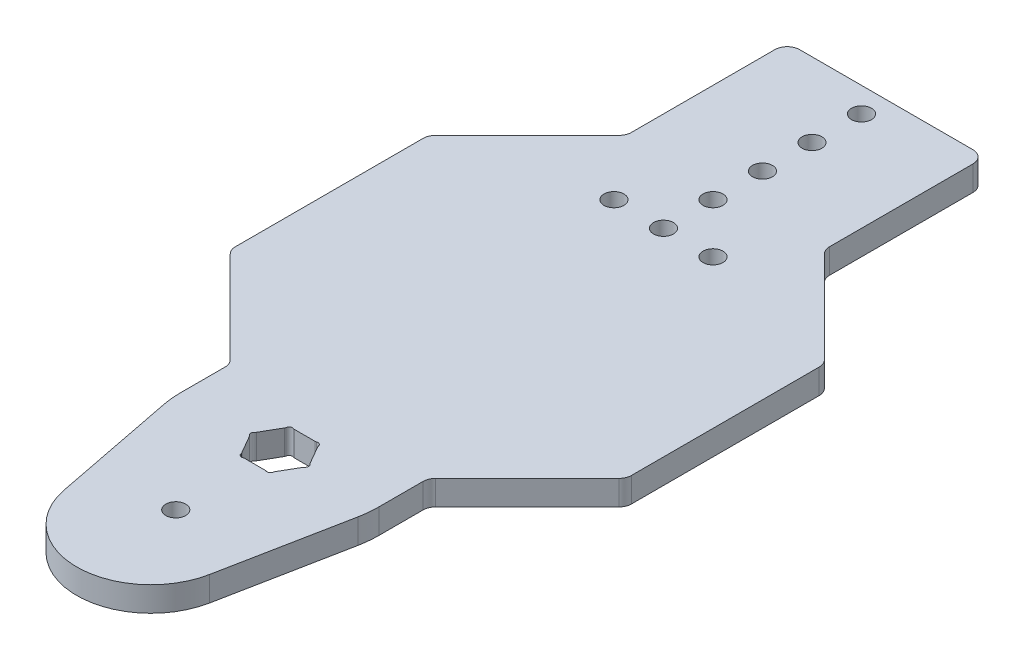
SolidWorks part; units mm, degrees
ref_plane "Front Plane" through (0, 0, 0) normal (0, 0, 1) x (1, 0, 0)
ref_plane "Top Plane" through (0, 0, 0) normal (0, 1, 0) x (1, 0, 0)
ref_plane "Right Plane" through (0, 0, 0) normal (1, 0, 0) x (0, 0, -1)
ref_plane "Plane1" through (0, 0, 0) normal (0, -1, 0) x (1, 0, 0)
sketch "Sketch1" plane through (0, 0, 0) normal (0, -1, 0) x (1, 0, 0)
  line L0 (-50.8, 24.0849) -> (-50.8, -24.0849)
  line L1 (-49.8701, -26.3299) -> (-26.3299, -49.8701)
  line L2 (-25.4, -52.1151) -> (-25.4, -88.9)
  line L3 (-22.225, -92.075) -> (22.225, -92.075)
  line L4 (25.4, -88.9) -> (25.4, -52.1151)
  line L5 (26.3299, -49.8701) -> (49.8701, -26.3299)
  line L6 (50.8, -24.0849) -> (50.8, 24.0849)
  line L7 (49.8701, 26.3299) -> (26.3299, 49.8701)
  line L8 (25.4, 52.1151) -> (25.4, 63.5)
  line L9 (24.9259, 68.3846) -> (18.6944, 100.1835)
  line L10 (-18.6944, 100.1835) -> (-24.9259, 68.3846)
  line L11 (-25.4, 63.5) -> (-25.4, 52.1151)
  line L12 (-26.3299, 49.8701) -> (-49.8701, 26.3299)
  line L13 (-6.8725, 64.4235) -> (-4.236, 68.99)
  line L14 (-2.6365, 69.9135) -> (2.6365, 69.9135)
  line L15 (4.236, 68.99) -> (6.8725, 64.4235)
  line L16 (6.8725, 62.5765) -> (4.236, 58.01)
  line L17 (2.6365, 57.0865) -> (-2.6365, 57.0865)
  line L18 (-4.236, 58.01) -> (-6.8725, 62.5765)
  arc A0 (-50.8, -24.0849) -> (-49.8701, -26.3299) centre (-47.625, -24.0849) ccw
  arc A1 (-26.3299, -49.8701) -> (-25.4, -52.1151) centre (-28.575, -52.1151) cw
  arc A2 (-25.4, -88.9) -> (-22.225, -92.075) centre (-22.225, -88.9) ccw
  arc A3 (22.225, -92.075) -> (25.4, -88.9) centre (22.225, -88.9) ccw
  arc A4 (25.4, -52.1151) -> (26.3299, -49.8701) centre (28.575, -52.1151) cw
  arc A5 (49.8701, -26.3299) -> (50.8, -24.0849) centre (47.625, -24.0849) ccw
  arc A6 (50.8, 24.0849) -> (49.8701, 26.3299) centre (47.625, 24.0849) ccw
  arc A7 (26.3299, 49.8701) -> (25.4, 52.1151) centre (28.575, 52.1151) cw
  arc A8 (25.4, 63.5) -> (24.9259, 68.3846) centre (0, 63.5) ccw
  arc A9 (18.6944, 100.1835) -> (-18.6944, 100.1835) centre (0, 96.52) ccw
  arc A10 (-24.9259, 68.3846) -> (-25.4, 63.5) centre (0, 63.5) ccw
  arc A11 (-25.4, 52.1151) -> (-26.3299, 49.8701) centre (-28.575, 52.1151) cw
  arc A12 (-49.8701, 26.3299) -> (-50.8, 24.0849) centre (-47.625, 24.0849) ccw
  circle A13 centre (0, 90.17) radius 2.5527
  circle A14 centre (0, -85.725) radius 2.5527
  circle A15 centre (0, -73.025) radius 2.5527
  circle A16 centre (0, -60.325) radius 2.5527
  circle A17 centre (0, -47.625) radius 2.5527
  circle A18 centre (0, -34.925) radius 2.5527
  circle A19 centre (-12.7, -34.925) radius 2.5527
  circle A20 centre (12.7, -34.925) radius 2.5527
  arc A21 (-7.0678, 62.8025) -> (-7.0678, 64.1975) centre (-6.5167, 63.5) cw
  arc A22 (-7.0678, 64.1975) -> (-6.8725, 64.4235) centre (-7.5599, 64.8203) ccw
  arc A23 (-4.236, 68.99) -> (-4.138, 69.2721) centre (-4.9234, 69.3869) ccw
  arc A24 (-4.138, 69.2721) -> (-2.9298, 69.9697) centre (-3.2583, 69.1436) cw
  arc A25 (-2.9298, 69.9697) -> (-2.6365, 69.9135) centre (-2.6365, 70.7073) ccw
  arc A26 (2.6365, 69.9135) -> (2.9298, 69.9697) centre (2.6365, 70.7073) ccw
  arc A27 (2.9298, 69.9697) -> (4.138, 69.2721) centre (3.2583, 69.1436) cw
  arc A28 (4.138, 69.2721) -> (4.236, 68.99) centre (4.9234, 69.3869) ccw
  arc A29 (6.8725, 64.4235) -> (7.0678, 64.1975) centre (7.5599, 64.8203) ccw
  arc A30 (7.0678, 64.1975) -> (7.0678, 62.8025) centre (6.5167, 63.5) cw
  arc A31 (7.0678, 62.8025) -> (6.8725, 62.5765) centre (7.5599, 62.1797) ccw
  arc A32 (4.236, 58.01) -> (4.138, 57.7279) centre (4.9234, 57.6131) ccw
  arc A33 (4.138, 57.7279) -> (2.9298, 57.0303) centre (3.2583, 57.8564) cw
  arc A34 (2.9298, 57.0303) -> (2.6365, 57.0865) centre (2.6365, 56.2928) ccw
  arc A35 (-2.6365, 57.0865) -> (-2.9298, 57.0303) centre (-2.6365, 56.2928) ccw
  arc A36 (-2.9298, 57.0303) -> (-4.138, 57.7279) centre (-3.2583, 57.8564) cw
  arc A37 (-4.138, 57.7279) -> (-4.236, 58.01) centre (-4.9234, 57.6131) ccw
  arc A38 (-6.8725, 62.5765) -> (-7.0678, 62.8025) centre (-7.5599, 62.1797) ccw
  dimension "D1" = 5.1054
  dimension "D2" = 5.1054
  dimension "D3" = 5.1054
  dimension "D4" = 5.1054
  dimension "D5" = 5.1054
  dimension "D6" = 5.1054
  dimension "D7" = 5.1054
  dimension "D8" = 5.1054
  dimension "D9" = 3.175
  dimension "D10" = 3.175
  dimension "D11" = 38.1
  dimension "D12" = 43.2401
  dimension "D13" = 63.5
  dimension "D14" = 6.35
  dimension "D15" = 19.05
  dimension "D16" = 31.75
  dimension "D17" = 44.45
  dimension "D18" = 57.15
  dimension "D19" = 182.245
extrude "Boss-Extrude1" add sketch "Sketch1" against normal blind 6.35
